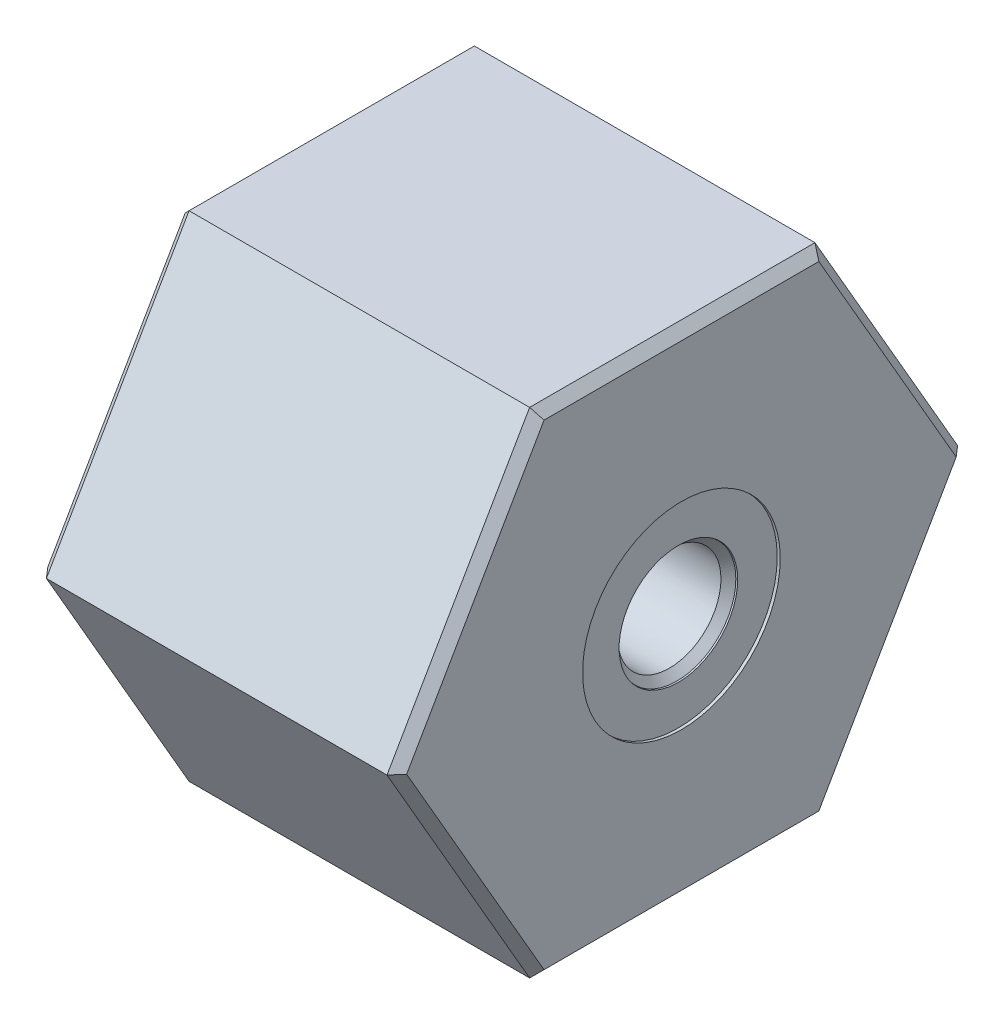
SolidWorks part; units mm, degrees
material "Alloy Steel"
ref_plane "Front Plane" through (0, 0, 0) normal (0, 0, 1) x (1, 0, 0)
ref_plane "Top Plane" through (0, 0, 0) normal (0, 1, 0) x (1, 0, 0)
ref_plane "Right Plane" through (0, 0, 0) normal (1, 0, 0) x (0, 0, -1)
sketch "Sketch1" plane through (0, 0, 0) normal (1, 0, 0) x (0, 0, -1)
  line L1 (11.9151, 20.6375) -> (-11.9151, 20.6375)
  line L2 (-11.9151, 20.6375) -> (-23.8301, 0)
  line L3 (-23.8301, 0) -> (-11.9151, -20.6375)
  line L4 (-11.9151, -20.6375) -> (11.9151, -20.6375)
  line L5 (11.9151, -20.6375) -> (23.8301, 0)
  line L6 (23.8301, 0) -> (11.9151, 20.6375)
  circle A0 centre (0, 0) radius 20.6375 construction
  dimension "D1" = 41.275
extrude "Extrude1" add sketch "Sketch1" along normal blind 29.972
sketch "Sketch2" plane through (0, 0, 0) normal (0, 0, 1) x (1, 0, 0)
  line L0 (0, 16.7513) -> (0, 0)
  line L1 (0, 20.6375) -> (0, 0) construction
  line L2 (29.972, 20.6375) -> (29.972, 0) construction
  line L3 (29.972, 8.255) -> (29.718, 8.255)
  line L4 (29.718, 8.255) -> (29.718, 4.953)
  line L5 (29.718, 4.953) -> (29.591, 4.926)
  line L6 (29.591, 4.926) -> (28.9703, 4.3053)
  line L7 (21.4884, 14.9352) -> (16.4592, 14.9352)
  line L8 (16.4592, 14.9352) -> (16.4592, 16.7513)
  line L9 (21.4884, 14.9352) -> (21.4884, 5.0673)
  line L10 (16.4592, 16.7513) -> (0, 16.7513)
  line L11 (0, 0) -> (34.3281, 0) construction
  line L12 (21.4884, 5.0673) -> (22.2504, 4.3053)
  line L13 (22.2504, 4.3053) -> (28.9703, 4.3053)
  line L14 (29.972, 8.255) -> (29.972, 0)
  line L15 (0, 0) -> (29.972, 0)
  dimension "D1" = 33.5026
  dimension "D2" = 16.4592
  dimension "D3" = 29.8704
  dimension "D4" = 0.254
  dimension "D5" = 16.51
  dimension "D6" = 45
  dimension "D7" = 0.127
  dimension "D8" = 12
  dimension "D9" = 8.6106
  dimension "D10" = 45
  dimension "D11" = 10.1346
  dimension "D12" = 21.4884
  dimension "D13" = 9.906
revolve "Cut-Revolve1" cut sketch "Sketch2" angle 360 about L11
chamfer "Chamfer1" distance 0.508 angle 45 1 edges at (0, 0, -16.7513)
chamfer "Chamfer3" distance 0.762 angle 45 6 edges at (0, 10.3188, 17.8726) (0, -10.3188, 17.8726) (0, 20.6375, 0) (0, 10.3188, -17.8726) (0, -10.3187, -17.8726) (0, -20.6375, 0)
chamfer "Chamfer4" distance 0.762 angle 45 6 edges at (29.972, 10.3188, 17.8726) (29.972, 20.6375, 0) (29.972, -10.3188, 17.8726) (29.972, 10.3188, -17.8726) (29.972, -10.3187, -17.8726) (29.972, -20.6375, 0)
fillet "Fillet1" radius 0.508 1 edges at (16.4592, 0, -16.7513)
